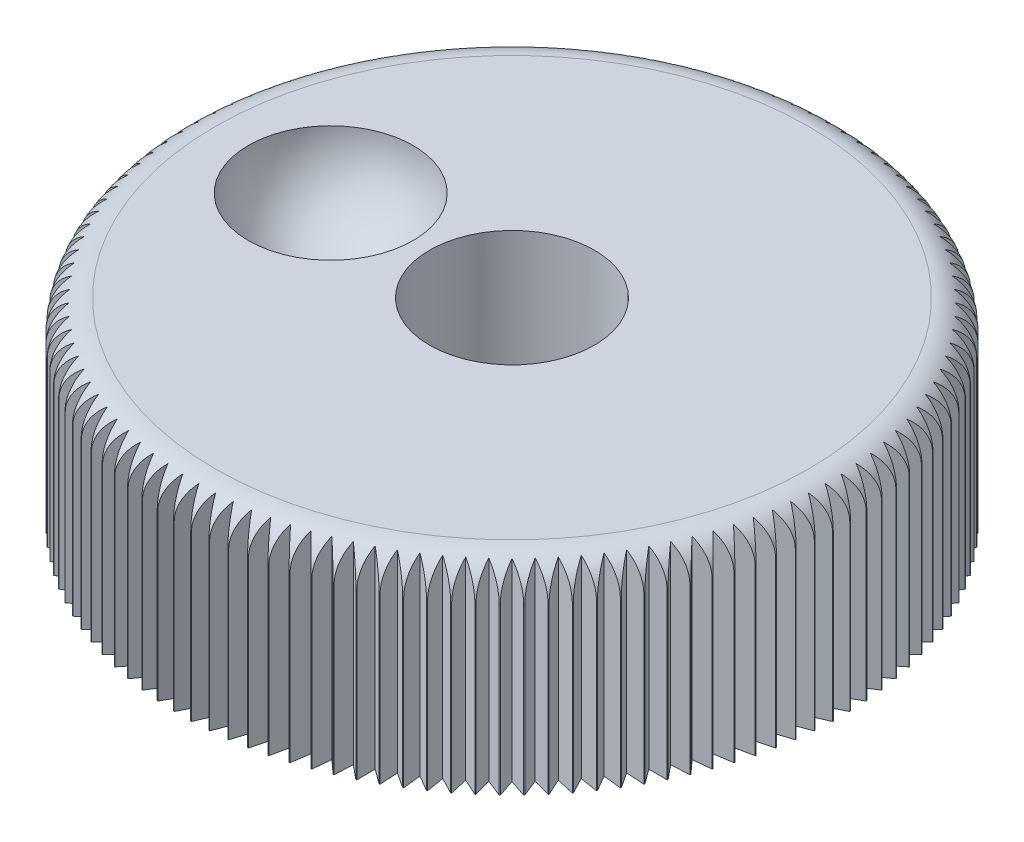
SolidWorks part; units mm, degrees
ref_plane "Спереди" through (0, 0, 0) normal (0, 0, 1) x (1, 0, 0)
ref_plane "Сверху" through (0, 0, 0) normal (0, 1, 0) x (1, 0, 0)
ref_plane "Справа" through (0, 0, 0) normal (1, 0, 0) x (0, 0, -1)
sketch "Эскиз1" plane through (0, 0, 0) normal (0, 1, 0) x (1, 0, 0)
  circle A0 centre (0, 0) radius 6
  dimension "D1" = 12
extrude "Бобышка-Вытянуть1" add sketch "Эскиз1" along normal blind 10
ref_plane "Плоскость1" through (0, 7.5, 0) normal (0, 1, 0) x (1, 0, 0)
sketch "Эскиз2" plane through (0, 7.5, 0) normal (0, 1, 0) x (1, 0, 0)
  circle A0 centre (0, 0) radius 20
  dimension "D1" = 40
extrude "Бобышка-Вытянуть2" add sketch "Эскиз2" along normal blind 12
fillet "Скругление1" radius 2 1 edges at (0, 19.5, 20)
sketch "Эскиз3" plane through (0, 7.5, 0) normal (0, -1, 0) x (1, 0, 0)
  line L0 (0, -20) -> (0, 20) construction
  line L1 (0, -20) -> (0, -21) construction
  line L2 (0, -21) -> (-0.5, -19.9937)
  line L3 (0, -21) -> (0.5, -19.9937)
  line L4 (0.5, -19.9937) -> (0, -19)
  line L5 (0, -19) -> (-0.5, -19.9937)
  line L6 (-1.0991, -20.9712) -> (-0.5471, -19.9925)
  line L7 (-1.0991, -20.9712) -> (-1.5457, -19.9402)
  line L8 (-0.9944, -18.974) -> (-1.5457, -19.9402)
  line L9 (-0.5471, -19.9925) -> (-0.9944, -18.974)
  line L10 (-2.1951, -20.885) -> (-1.5927, -19.9365)
  line L11 (-2.1951, -20.885) -> (-2.5872, -19.832)
  line L12 (-1.986, -18.8959) -> (-2.5872, -19.832)
  line L13 (-1.5927, -19.9365) -> (-1.986, -18.8959)
  line L14 (-3.2851, -20.7415) -> (-2.6339, -19.8258)
  line L15 (-3.2851, -20.7415) -> (-3.6216, -19.6694)
  line L16 (-2.9723, -18.7661) -> (-3.6216, -19.6694)
  line L17 (-2.6339, -19.8258) -> (-2.9723, -18.7661)
  line L18 (-4.3661, -20.5411) -> (-3.6679, -19.6608)
  line L19 (-4.3661, -20.5411) -> (-4.646, -19.4529)
  line L20 (-3.9503, -18.5848) -> (-4.646, -19.4529)
  line L21 (-3.6679, -19.6608) -> (-3.9503, -18.5848)
  line L22 (-5.4352, -20.2844) -> (-4.6918, -19.4419)
  line L23 (-5.4352, -20.2844) -> (-5.6577, -19.1831)
  line L24 (-4.9176, -18.3526) -> (-5.6577, -19.1831)
  line L25 (-4.6918, -19.4419) -> (-4.9176, -18.3526)
  line L26 (-6.4894, -19.9722) -> (-5.7029, -19.1697)
  line L27 (-6.4894, -19.9722) -> (-6.6539, -18.8607)
  line L28 (-5.8713, -18.0701) -> (-6.6539, -18.8607)
  line L29 (-5.7029, -19.1697) -> (-5.8713, -18.0701)
  line L30 (-7.5257, -19.6052) -> (-6.6983, -18.845)
  line L31 (-7.5257, -19.6052) -> (-7.6319, -18.4866)
  line L32 (-6.809, -17.738) -> (-7.6319, -18.4866)
  line L33 (-6.6983, -18.845) -> (-6.809, -17.738)
  line L34 (-8.5415, -19.1845) -> (-7.6754, -18.4686)
  line L35 (-8.5415, -19.1845) -> (-8.589, -18.0618)
  line L36 (-7.728, -17.3574) -> (-8.589, -18.0618)
  line L37 (-7.6754, -18.4686) -> (-7.728, -17.3574)
  line L38 (-9.5338, -18.7111) -> (-8.6315, -18.0416)
  line L39 (-9.5338, -18.7111) -> (-9.5225, -17.5876)
  line L40 (-8.6258, -16.9291) -> (-9.5225, -17.5876)
  line L41 (-8.6315, -18.0416) -> (-8.6258, -16.9291)
  line L42 (-10.5, -18.1865) -> (-9.5639, -17.5651)
  line L43 (-10.5, -18.1865) -> (-10.4299, -17.0651)
  line L44 (-9.5, -16.4545) -> (-10.4299, -17.0651)
  line L45 (-9.5639, -17.5651) -> (-9.5, -16.4545)
  line L46 (-11.4374, -17.6121) -> (-10.47, -17.0405)
  line L47 (-11.4374, -17.6121) -> (-11.3087, -16.4958)
  line L48 (-10.3481, -15.9347) -> (-11.3087, -16.4958)
  line L49 (-10.47, -17.0405) -> (-10.3481, -15.9347)
  line L50 (-12.3435, -16.9894) -> (-11.3475, -16.4692)
  line L51 (-12.3435, -16.9894) -> (-12.1565, -15.8814)
  line L52 (-11.1679, -15.3713) -> (-12.1565, -15.8814)
  line L53 (-11.3475, -16.4692) -> (-11.1679, -15.3713)
  line L54 (-13.2157, -16.3201) -> (-12.1939, -15.8527)
  line L55 (-13.2157, -16.3201) -> (-12.971, -15.2234)
  line L56 (-11.9571, -14.7658) -> (-12.971, -15.2234)
  line L57 (-12.1939, -15.8527) -> (-11.9571, -14.7658)
  line L58 (-14.0517, -15.606) -> (-13.0069, -15.1928)
  line L59 (-14.0517, -15.606) -> (-13.75, -14.5237)
  line L60 (-12.7135, -14.1198) -> (-13.75, -14.5237)
  line L61 (-13.0069, -15.1928) -> (-12.7135, -14.1198)
  line L62 (-14.8492, -14.8492) -> (-13.7842, -14.4913)
  line L63 (-14.8492, -14.8492) -> (-14.4913, -13.7842)
  line L64 (-13.435, -13.435) -> (-14.4913, -13.7842)
  line L65 (-13.7842, -14.4913) -> (-13.435, -13.435)
  line L66 (-15.606, -14.0517) -> (-14.5237, -13.75)
  line L67 (-15.606, -14.0517) -> (-15.1928, -13.0069)
  line L68 (-14.1198, -12.7135) -> (-15.1928, -13.0069)
  line L69 (-14.5237, -13.75) -> (-14.1198, -12.7135)
  line L70 (-16.3201, -13.2157) -> (-15.2234, -12.971)
  line L71 (-16.3201, -13.2157) -> (-15.8527, -12.1939)
  line L72 (-14.7658, -11.9571) -> (-15.8527, -12.1939)
  line L73 (-15.2234, -12.971) -> (-14.7658, -11.9571)
  line L74 (-16.9894, -12.3435) -> (-15.8814, -12.1565)
  line L75 (-16.9894, -12.3435) -> (-16.4692, -11.3475)
  line L76 (-15.3713, -11.1679) -> (-16.4692, -11.3475)
  line L77 (-15.8814, -12.1565) -> (-15.3713, -11.1679)
  line L78 (-17.6121, -11.4374) -> (-16.4958, -11.3087)
  line L79 (-17.6121, -11.4374) -> (-17.0405, -10.47)
  line L80 (-15.9347, -10.3481) -> (-17.0405, -10.47)
  line L81 (-16.4958, -11.3087) -> (-15.9347, -10.3481)
  line L82 (-18.1865, -10.5) -> (-17.0651, -10.4299)
  line L83 (-18.1865, -10.5) -> (-17.5651, -9.5639)
  line L84 (-16.4545, -9.5) -> (-17.5651, -9.5639)
  line L85 (-17.0651, -10.4299) -> (-16.4545, -9.5)
  line L86 (-18.7111, -9.5338) -> (-17.5876, -9.5225)
  line L87 (-18.7111, -9.5338) -> (-18.0416, -8.6315)
  line L88 (-16.9291, -8.6258) -> (-18.0416, -8.6315)
  line L89 (-17.5876, -9.5225) -> (-16.9291, -8.6258)
  line L90 (-19.1845, -8.5415) -> (-18.0618, -8.589)
  line L91 (-19.1845, -8.5415) -> (-18.4686, -7.6754)
  line L92 (-17.3574, -7.728) -> (-18.4686, -7.6754)
  line L93 (-18.0618, -8.589) -> (-17.3574, -7.728)
  line L94 (-19.6052, -7.5257) -> (-18.4866, -7.6319)
  line L95 (-19.6052, -7.5257) -> (-18.845, -6.6983)
  line L96 (-17.738, -6.809) -> (-18.845, -6.6983)
  line L97 (-18.4866, -7.6319) -> (-17.738, -6.809)
  line L98 (-19.9722, -6.4894) -> (-18.8607, -6.6539)
  line L99 (-19.9722, -6.4894) -> (-19.1697, -5.7029)
  line L100 (-18.0701, -5.8713) -> (-19.1697, -5.7029)
  line L101 (-18.8607, -6.6539) -> (-18.0701, -5.8713)
  line L102 (-20.2844, -5.4352) -> (-19.1831, -5.6577)
  line L103 (-20.2844, -5.4352) -> (-19.4419, -4.6918)
  line L104 (-18.3526, -4.9176) -> (-19.4419, -4.6918)
  line L105 (-19.1831, -5.6577) -> (-18.3526, -4.9176)
  line L106 (-20.5411, -4.3661) -> (-19.4529, -4.646)
  line L107 (-20.5411, -4.3661) -> (-19.6608, -3.6679)
  line L108 (-18.5848, -3.9503) -> (-19.6608, -3.6679)
  line L109 (-19.4529, -4.646) -> (-18.5848, -3.9503)
  line L110 (-20.7415, -3.2851) -> (-19.6694, -3.6216)
  line L111 (-20.7415, -3.2851) -> (-19.8258, -2.6339)
  line L112 (-18.7661, -2.9723) -> (-19.8258, -2.6339)
  line L113 (-19.6694, -3.6216) -> (-18.7661, -2.9723)
  line L114 (-20.885, -2.1951) -> (-19.832, -2.5872)
  line L115 (-20.885, -2.1951) -> (-19.9365, -1.5927)
  line L116 (-18.8959, -1.986) -> (-19.9365, -1.5927)
  line L117 (-19.832, -2.5872) -> (-18.8959, -1.986)
  line L118 (-20.9712, -1.0991) -> (-19.9402, -1.5457)
  line L119 (-20.9712, -1.0991) -> (-19.9925, -0.5471)
  line L120 (-18.974, -0.9944) -> (-19.9925, -0.5471)
  line L121 (-19.9402, -1.5457) -> (-18.974, -0.9944)
  line L122 (-21, 0) -> (-19.9937, -0.5)
  line L123 (-21, 0) -> (-19.9937, 0.5)
  line L124 (-19, 0) -> (-19.9937, 0.5)
  line L125 (-19.9937, -0.5) -> (-19, 0)
  line L126 (-20.9712, 1.0991) -> (-19.9925, 0.5471)
  line L127 (-20.9712, 1.0991) -> (-19.9402, 1.5457)
  line L128 (-18.974, 0.9944) -> (-19.9402, 1.5457)
  line L129 (-19.9925, 0.5471) -> (-18.974, 0.9944)
  line L130 (-20.885, 2.1951) -> (-19.9365, 1.5927)
  line L131 (-20.885, 2.1951) -> (-19.832, 2.5872)
  line L132 (-18.8959, 1.986) -> (-19.832, 2.5872)
  line L133 (-19.9365, 1.5927) -> (-18.8959, 1.986)
  line L134 (-20.7415, 3.2851) -> (-19.8258, 2.6339)
  line L135 (-20.7415, 3.2851) -> (-19.6694, 3.6216)
  line L136 (-18.7661, 2.9723) -> (-19.6694, 3.6216)
  line L137 (-19.8258, 2.6339) -> (-18.7661, 2.9723)
  line L138 (-20.5411, 4.3661) -> (-19.6608, 3.6679)
  line L139 (-20.5411, 4.3661) -> (-19.4529, 4.646)
  line L140 (-18.5848, 3.9503) -> (-19.4529, 4.646)
  line L141 (-19.6608, 3.6679) -> (-18.5848, 3.9503)
  line L142 (-20.2844, 5.4352) -> (-19.4419, 4.6918)
  line L143 (-20.2844, 5.4352) -> (-19.1831, 5.6577)
  line L144 (-18.3526, 4.9176) -> (-19.1831, 5.6577)
  line L145 (-19.4419, 4.6918) -> (-18.3526, 4.9176)
  line L146 (-19.9722, 6.4894) -> (-19.1697, 5.7029)
  line L147 (-19.9722, 6.4894) -> (-18.8607, 6.6539)
  line L148 (-18.0701, 5.8713) -> (-18.8607, 6.6539)
  line L149 (-19.1697, 5.7029) -> (-18.0701, 5.8713)
  line L150 (-19.6052, 7.5257) -> (-18.845, 6.6983)
  line L151 (-19.6052, 7.5257) -> (-18.4866, 7.6319)
  line L152 (-17.738, 6.809) -> (-18.4866, 7.6319)
  line L153 (-18.845, 6.6983) -> (-17.738, 6.809)
  line L154 (-19.1845, 8.5415) -> (-18.4686, 7.6754)
  line L155 (-19.1845, 8.5415) -> (-18.0618, 8.589)
  line L156 (-17.3574, 7.728) -> (-18.0618, 8.589)
  line L157 (-18.4686, 7.6754) -> (-17.3574, 7.728)
  line L158 (-18.7111, 9.5338) -> (-18.0416, 8.6315)
  line L159 (-18.7111, 9.5338) -> (-17.5876, 9.5225)
  line L160 (-16.9291, 8.6258) -> (-17.5876, 9.5225)
  line L161 (-18.0416, 8.6315) -> (-16.9291, 8.6258)
  line L162 (-18.1865, 10.5) -> (-17.5651, 9.5639)
  line L163 (-18.1865, 10.5) -> (-17.0651, 10.4299)
  line L164 (-16.4545, 9.5) -> (-17.0651, 10.4299)
  line L165 (-17.5651, 9.5639) -> (-16.4545, 9.5)
  line L166 (-17.6121, 11.4374) -> (-17.0405, 10.47)
  line L167 (-17.6121, 11.4374) -> (-16.4958, 11.3087)
  line L168 (-15.9347, 10.3481) -> (-16.4958, 11.3087)
  line L169 (-17.0405, 10.47) -> (-15.9347, 10.3481)
  line L170 (-16.9894, 12.3435) -> (-16.4692, 11.3475)
  line L171 (-16.9894, 12.3435) -> (-15.8814, 12.1565)
  line L172 (-15.3713, 11.1679) -> (-15.8814, 12.1565)
  line L173 (-16.4692, 11.3475) -> (-15.3713, 11.1679)
  line L174 (-16.3201, 13.2157) -> (-15.8527, 12.1939)
  line L175 (-16.3201, 13.2157) -> (-15.2234, 12.971)
  line L176 (-14.7658, 11.9571) -> (-15.2234, 12.971)
  line L177 (-15.8527, 12.1939) -> (-14.7658, 11.9571)
  line L178 (-15.606, 14.0517) -> (-15.1928, 13.0069)
  line L179 (-15.606, 14.0517) -> (-14.5237, 13.75)
  line L180 (-14.1198, 12.7135) -> (-14.5237, 13.75)
  line L181 (-15.1928, 13.0069) -> (-14.1198, 12.7135)
  line L182 (-14.8492, 14.8492) -> (-14.4913, 13.7842)
  line L183 (-14.8492, 14.8492) -> (-13.7842, 14.4913)
  line L184 (-13.435, 13.435) -> (-13.7842, 14.4913)
  line L185 (-14.4913, 13.7842) -> (-13.435, 13.435)
  line L186 (-14.0517, 15.606) -> (-13.75, 14.5237)
  line L187 (-14.0517, 15.606) -> (-13.0069, 15.1928)
  line L188 (-12.7135, 14.1198) -> (-13.0069, 15.1928)
  line L189 (-13.75, 14.5237) -> (-12.7135, 14.1198)
  line L190 (-13.2157, 16.3201) -> (-12.971, 15.2234)
  line L191 (-13.2157, 16.3201) -> (-12.1939, 15.8527)
  line L192 (-11.9571, 14.7658) -> (-12.1939, 15.8527)
  line L193 (-12.971, 15.2234) -> (-11.9571, 14.7658)
  line L194 (-12.3435, 16.9894) -> (-12.1565, 15.8814)
  line L195 (-12.3435, 16.9894) -> (-11.3475, 16.4692)
  line L196 (-11.1679, 15.3713) -> (-11.3475, 16.4692)
  line L197 (-12.1565, 15.8814) -> (-11.1679, 15.3713)
  line L198 (-11.4374, 17.6121) -> (-11.3087, 16.4958)
  line L199 (-11.4374, 17.6121) -> (-10.47, 17.0405)
  line L200 (-10.3481, 15.9347) -> (-10.47, 17.0405)
  line L201 (-11.3087, 16.4958) -> (-10.3481, 15.9347)
  line L202 (-10.5, 18.1865) -> (-10.4299, 17.0651)
  line L203 (-10.5, 18.1865) -> (-9.5639, 17.5651)
  line L204 (-9.5, 16.4545) -> (-9.5639, 17.5651)
  line L205 (-10.4299, 17.0651) -> (-9.5, 16.4545)
  line L206 (-9.5338, 18.7111) -> (-9.5225, 17.5876)
  line L207 (-9.5338, 18.7111) -> (-8.6315, 18.0416)
  line L208 (-8.6258, 16.9291) -> (-8.6315, 18.0416)
  line L209 (-9.5225, 17.5876) -> (-8.6258, 16.9291)
  line L210 (-8.5415, 19.1845) -> (-8.589, 18.0618)
  line L211 (-8.5415, 19.1845) -> (-7.6754, 18.4686)
  line L212 (-7.728, 17.3574) -> (-7.6754, 18.4686)
  line L213 (-8.589, 18.0618) -> (-7.728, 17.3574)
  line L214 (-7.5257, 19.6052) -> (-7.6319, 18.4866)
  line L215 (-7.5257, 19.6052) -> (-6.6983, 18.845)
  line L216 (-6.809, 17.738) -> (-6.6983, 18.845)
  line L217 (-7.6319, 18.4866) -> (-6.809, 17.738)
  line L218 (-6.4894, 19.9722) -> (-6.6539, 18.8607)
  line L219 (-6.4894, 19.9722) -> (-5.7029, 19.1697)
  line L220 (-5.8713, 18.0701) -> (-5.7029, 19.1697)
  line L221 (-6.6539, 18.8607) -> (-5.8713, 18.0701)
  line L222 (-5.4352, 20.2844) -> (-5.6577, 19.1831)
  line L223 (-5.4352, 20.2844) -> (-4.6918, 19.4419)
  line L224 (-4.9176, 18.3526) -> (-4.6918, 19.4419)
  line L225 (-5.6577, 19.1831) -> (-4.9176, 18.3526)
  line L226 (-4.3661, 20.5411) -> (-4.646, 19.4529)
  line L227 (-4.3661, 20.5411) -> (-3.6679, 19.6608)
  line L228 (-3.9503, 18.5848) -> (-3.6679, 19.6608)
  line L229 (-4.646, 19.4529) -> (-3.9503, 18.5848)
  line L230 (-3.2851, 20.7415) -> (-3.6216, 19.6694)
  line L231 (-3.2851, 20.7415) -> (-2.6339, 19.8258)
  line L232 (-2.9723, 18.7661) -> (-2.6339, 19.8258)
  line L233 (-3.6216, 19.6694) -> (-2.9723, 18.7661)
  line L234 (-2.1951, 20.885) -> (-2.5872, 19.832)
  line L235 (-2.1951, 20.885) -> (-1.5927, 19.9365)
  line L236 (-1.986, 18.8959) -> (-1.5927, 19.9365)
  line L237 (-2.5872, 19.832) -> (-1.986, 18.8959)
  line L238 (-1.0991, 20.9712) -> (-1.5457, 19.9402)
  line L239 (-1.0991, 20.9712) -> (-0.5471, 19.9925)
  line L240 (-0.9944, 18.974) -> (-0.5471, 19.9925)
  line L241 (-1.5457, 19.9402) -> (-0.9944, 18.974)
  line L242 (0, 21) -> (-0.5, 19.9937)
  line L243 (0, 21) -> (0.5, 19.9937)
  line L244 (0, 19) -> (0.5, 19.9937)
  line L245 (-0.5, 19.9937) -> (0, 19)
  line L246 (1.0991, 20.9712) -> (0.5471, 19.9925)
  line L247 (1.0991, 20.9712) -> (1.5457, 19.9402)
  line L248 (0.9944, 18.974) -> (1.5457, 19.9402)
  line L249 (0.5471, 19.9925) -> (0.9944, 18.974)
  line L250 (2.1951, 20.885) -> (1.5927, 19.9365)
  line L251 (2.1951, 20.885) -> (2.5872, 19.832)
  line L252 (1.986, 18.8959) -> (2.5872, 19.832)
  line L253 (1.5927, 19.9365) -> (1.986, 18.8959)
  line L254 (3.2851, 20.7415) -> (2.6339, 19.8258)
  line L255 (3.2851, 20.7415) -> (3.6216, 19.6694)
  line L256 (2.9723, 18.7661) -> (3.6216, 19.6694)
  line L257 (2.6339, 19.8258) -> (2.9723, 18.7661)
  line L258 (4.3661, 20.5411) -> (3.6679, 19.6608)
  line L259 (4.3661, 20.5411) -> (4.646, 19.4529)
  line L260 (3.9503, 18.5848) -> (4.646, 19.4529)
  line L261 (3.6679, 19.6608) -> (3.9503, 18.5848)
  line L262 (5.4352, 20.2844) -> (4.6918, 19.4419)
  line L263 (5.4352, 20.2844) -> (5.6577, 19.1831)
  line L264 (4.9176, 18.3526) -> (5.6577, 19.1831)
  line L265 (4.6918, 19.4419) -> (4.9176, 18.3526)
  line L266 (6.4894, 19.9722) -> (5.7029, 19.1697)
  line L267 (6.4894, 19.9722) -> (6.6539, 18.8607)
  line L268 (5.8713, 18.0701) -> (6.6539, 18.8607)
  line L269 (5.7029, 19.1697) -> (5.8713, 18.0701)
  line L270 (7.5257, 19.6052) -> (6.6983, 18.845)
  line L271 (7.5257, 19.6052) -> (7.6319, 18.4866)
  line L272 (6.809, 17.738) -> (7.6319, 18.4866)
  line L273 (6.6983, 18.845) -> (6.809, 17.738)
  line L274 (8.5415, 19.1845) -> (7.6754, 18.4686)
  line L275 (8.5415, 19.1845) -> (8.589, 18.0618)
  line L276 (7.728, 17.3574) -> (8.589, 18.0618)
  line L277 (7.6754, 18.4686) -> (7.728, 17.3574)
  line L278 (9.5338, 18.7111) -> (8.6315, 18.0416)
  line L279 (9.5338, 18.7111) -> (9.5225, 17.5876)
  line L280 (8.6258, 16.9291) -> (9.5225, 17.5876)
  line L281 (8.6315, 18.0416) -> (8.6258, 16.9291)
  line L282 (10.5, 18.1865) -> (9.5639, 17.5651)
  line L283 (10.5, 18.1865) -> (10.4299, 17.0651)
  line L284 (9.5, 16.4545) -> (10.4299, 17.0651)
  line L285 (9.5639, 17.5651) -> (9.5, 16.4545)
  line L286 (11.4374, 17.6121) -> (10.47, 17.0405)
  line L287 (11.4374, 17.6121) -> (11.3087, 16.4958)
  line L288 (10.3481, 15.9347) -> (11.3087, 16.4958)
  line L289 (10.47, 17.0405) -> (10.3481, 15.9347)
  line L290 (12.3435, 16.9894) -> (11.3475, 16.4692)
  line L291 (12.3435, 16.9894) -> (12.1565, 15.8814)
  line L292 (11.1679, 15.3713) -> (12.1565, 15.8814)
  line L293 (11.3475, 16.4692) -> (11.1679, 15.3713)
  line L294 (13.2157, 16.3201) -> (12.1939, 15.8527)
  line L295 (13.2157, 16.3201) -> (12.971, 15.2234)
  line L296 (11.9571, 14.7658) -> (12.971, 15.2234)
  line L297 (12.1939, 15.8527) -> (11.9571, 14.7658)
  line L298 (14.0517, 15.606) -> (13.0069, 15.1928)
  line L299 (14.0517, 15.606) -> (13.75, 14.5237)
  line L300 (12.7135, 14.1198) -> (13.75, 14.5237)
  line L301 (13.0069, 15.1928) -> (12.7135, 14.1198)
  line L302 (14.8492, 14.8492) -> (13.7842, 14.4913)
  line L303 (14.8492, 14.8492) -> (14.4913, 13.7842)
  line L304 (13.435, 13.435) -> (14.4913, 13.7842)
  line L305 (13.7842, 14.4913) -> (13.435, 13.435)
  line L306 (15.606, 14.0517) -> (14.5237, 13.75)
  line L307 (15.606, 14.0517) -> (15.1928, 13.0069)
  line L308 (14.1198, 12.7135) -> (15.1928, 13.0069)
  line L309 (14.5237, 13.75) -> (14.1198, 12.7135)
  line L310 (16.3201, 13.2157) -> (15.2234, 12.971)
  line L311 (16.3201, 13.2157) -> (15.8527, 12.1939)
  line L312 (14.7658, 11.9571) -> (15.8527, 12.1939)
  line L313 (15.2234, 12.971) -> (14.7658, 11.9571)
  line L314 (16.9894, 12.3435) -> (15.8814, 12.1565)
  line L315 (16.9894, 12.3435) -> (16.4692, 11.3475)
  line L316 (15.3713, 11.1679) -> (16.4692, 11.3475)
  line L317 (15.8814, 12.1565) -> (15.3713, 11.1679)
  line L318 (17.6121, 11.4374) -> (16.4958, 11.3087)
  line L319 (17.6121, 11.4374) -> (17.0405, 10.47)
  line L320 (15.9347, 10.3481) -> (17.0405, 10.47)
  line L321 (16.4958, 11.3087) -> (15.9347, 10.3481)
  line L322 (18.1865, 10.5) -> (17.0651, 10.4299)
  line L323 (18.1865, 10.5) -> (17.5651, 9.5639)
  line L324 (16.4545, 9.5) -> (17.5651, 9.5639)
  line L325 (17.0651, 10.4299) -> (16.4545, 9.5)
  line L326 (18.7111, 9.5338) -> (17.5876, 9.5225)
  line L327 (18.7111, 9.5338) -> (18.0416, 8.6315)
  line L328 (16.9291, 8.6258) -> (18.0416, 8.6315)
  line L329 (17.5876, 9.5225) -> (16.9291, 8.6258)
  line L330 (19.1845, 8.5415) -> (18.0618, 8.589)
  line L331 (19.1845, 8.5415) -> (18.4686, 7.6754)
  line L332 (17.3574, 7.728) -> (18.4686, 7.6754)
  line L333 (18.0618, 8.589) -> (17.3574, 7.728)
  line L334 (19.6052, 7.5257) -> (18.4866, 7.6319)
  line L335 (19.6052, 7.5257) -> (18.845, 6.6983)
  line L336 (17.738, 6.809) -> (18.845, 6.6983)
  line L337 (18.4866, 7.6319) -> (17.738, 6.809)
  line L338 (19.9722, 6.4894) -> (18.8607, 6.6539)
  line L339 (19.9722, 6.4894) -> (19.1697, 5.7029)
  line L340 (18.0701, 5.8713) -> (19.1697, 5.7029)
  line L341 (18.8607, 6.6539) -> (18.0701, 5.8713)
  line L342 (20.2844, 5.4352) -> (19.1831, 5.6577)
  line L343 (20.2844, 5.4352) -> (19.4419, 4.6918)
  line L344 (18.3526, 4.9176) -> (19.4419, 4.6918)
  line L345 (19.1831, 5.6577) -> (18.3526, 4.9176)
  line L346 (20.5411, 4.3661) -> (19.4529, 4.646)
  line L347 (20.5411, 4.3661) -> (19.6608, 3.6679)
  line L348 (18.5848, 3.9503) -> (19.6608, 3.6679)
  line L349 (19.4529, 4.646) -> (18.5848, 3.9503)
  line L350 (20.7415, 3.2851) -> (19.6694, 3.6216)
  line L351 (20.7415, 3.2851) -> (19.8258, 2.6339)
  line L352 (18.7661, 2.9723) -> (19.8258, 2.6339)
  line L353 (19.6694, 3.6216) -> (18.7661, 2.9723)
  line L354 (20.885, 2.1951) -> (19.832, 2.5872)
  line L355 (20.885, 2.1951) -> (19.9365, 1.5927)
  line L356 (18.8959, 1.986) -> (19.9365, 1.5927)
  line L357 (19.832, 2.5872) -> (18.8959, 1.986)
  line L358 (20.9712, 1.0991) -> (19.9402, 1.5457)
  line L359 (20.9712, 1.0991) -> (19.9925, 0.5471)
  line L360 (18.974, 0.9944) -> (19.9925, 0.5471)
  line L361 (19.9402, 1.5457) -> (18.974, 0.9944)
  line L362 (21, 0) -> (19.9937, 0.5)
  line L363 (21, 0) -> (19.9937, -0.5)
  line L364 (19, 0) -> (19.9937, -0.5)
  line L365 (19.9937, 0.5) -> (19, 0)
  line L366 (20.9712, -1.0991) -> (19.9925, -0.5471)
  line L367 (20.9712, -1.0991) -> (19.9402, -1.5457)
  line L368 (18.974, -0.9944) -> (19.9402, -1.5457)
  line L369 (19.9925, -0.5471) -> (18.974, -0.9944)
  line L370 (20.885, -2.1951) -> (19.9365, -1.5927)
  line L371 (20.885, -2.1951) -> (19.832, -2.5872)
  line L372 (18.8959, -1.986) -> (19.832, -2.5872)
  line L373 (19.9365, -1.5927) -> (18.8959, -1.986)
  line L374 (20.7415, -3.2851) -> (19.8258, -2.6339)
  line L375 (20.7415, -3.2851) -> (19.6694, -3.6216)
  line L376 (18.7661, -2.9723) -> (19.6694, -3.6216)
  line L377 (19.8258, -2.6339) -> (18.7661, -2.9723)
  line L378 (20.5411, -4.3661) -> (19.6608, -3.6679)
  line L379 (20.5411, -4.3661) -> (19.4529, -4.646)
  line L380 (18.5848, -3.9503) -> (19.4529, -4.646)
  line L381 (19.6608, -3.6679) -> (18.5848, -3.9503)
  line L382 (20.2844, -5.4352) -> (19.4419, -4.6918)
  line L383 (20.2844, -5.4352) -> (19.1831, -5.6577)
  line L384 (18.3526, -4.9176) -> (19.1831, -5.6577)
  line L385 (19.4419, -4.6918) -> (18.3526, -4.9176)
  line L386 (19.9722, -6.4894) -> (19.1697, -5.7029)
  line L387 (19.9722, -6.4894) -> (18.8607, -6.6539)
  line L388 (18.0701, -5.8713) -> (18.8607, -6.6539)
  line L389 (19.1697, -5.7029) -> (18.0701, -5.8713)
  line L390 (19.6052, -7.5257) -> (18.845, -6.6983)
  line L391 (19.6052, -7.5257) -> (18.4866, -7.6319)
  line L392 (17.738, -6.809) -> (18.4866, -7.6319)
  line L393 (18.845, -6.6983) -> (17.738, -6.809)
  line L394 (19.1845, -8.5415) -> (18.4686, -7.6754)
  line L395 (19.1845, -8.5415) -> (18.0618, -8.589)
  line L396 (17.3574, -7.728) -> (18.0618, -8.589)
  line L397 (18.4686, -7.6754) -> (17.3574, -7.728)
  line L398 (18.7111, -9.5338) -> (18.0416, -8.6315)
  line L399 (18.7111, -9.5338) -> (17.5876, -9.5225)
  line L400 (16.9291, -8.6258) -> (17.5876, -9.5225)
  line L401 (18.0416, -8.6315) -> (16.9291, -8.6258)
  line L402 (18.1865, -10.5) -> (17.5651, -9.5639)
  line L403 (18.1865, -10.5) -> (17.0651, -10.4299)
  line L404 (16.4545, -9.5) -> (17.0651, -10.4299)
  line L405 (17.5651, -9.5639) -> (16.4545, -9.5)
  line L406 (17.6121, -11.4374) -> (17.0405, -10.47)
  line L407 (17.6121, -11.4374) -> (16.4958, -11.3087)
  line L408 (15.9347, -10.3481) -> (16.4958, -11.3087)
  line L409 (17.0405, -10.47) -> (15.9347, -10.3481)
  line L410 (16.9894, -12.3435) -> (16.4692, -11.3475)
  line L411 (16.9894, -12.3435) -> (15.8814, -12.1565)
  line L412 (15.3713, -11.1679) -> (15.8814, -12.1565)
  line L413 (16.4692, -11.3475) -> (15.3713, -11.1679)
  line L414 (16.3201, -13.2157) -> (15.8527, -12.1939)
  line L415 (16.3201, -13.2157) -> (15.2234, -12.971)
  line L416 (14.7658, -11.9571) -> (15.2234, -12.971)
  line L417 (15.8527, -12.1939) -> (14.7658, -11.9571)
  line L418 (15.606, -14.0517) -> (15.1928, -13.0069)
  line L419 (15.606, -14.0517) -> (14.5237, -13.75)
  line L420 (14.1198, -12.7135) -> (14.5237, -13.75)
  line L421 (15.1928, -13.0069) -> (14.1198, -12.7135)
  line L422 (14.8492, -14.8492) -> (14.4913, -13.7842)
  line L423 (14.8492, -14.8492) -> (13.7842, -14.4913)
  line L424 (13.435, -13.435) -> (13.7842, -14.4913)
  line L425 (14.4913, -13.7842) -> (13.435, -13.435)
  line L426 (14.0517, -15.606) -> (13.75, -14.5237)
  line L427 (14.0517, -15.606) -> (13.0069, -15.1928)
  line L428 (12.7135, -14.1198) -> (13.0069, -15.1928)
  line L429 (13.75, -14.5237) -> (12.7135, -14.1198)
  line L430 (13.2157, -16.3201) -> (12.971, -15.2234)
  line L431 (13.2157, -16.3201) -> (12.1939, -15.8527)
  line L432 (11.9571, -14.7658) -> (12.1939, -15.8527)
  line L433 (12.971, -15.2234) -> (11.9571, -14.7658)
  line L434 (12.3435, -16.9894) -> (12.1565, -15.8814)
  line L435 (12.3435, -16.9894) -> (11.3475, -16.4692)
  line L436 (11.1679, -15.3713) -> (11.3475, -16.4692)
  line L437 (12.1565, -15.8814) -> (11.1679, -15.3713)
  line L438 (11.4374, -17.6121) -> (11.3087, -16.4958)
  line L439 (11.4374, -17.6121) -> (10.47, -17.0405)
  line L440 (10.3481, -15.9347) -> (10.47, -17.0405)
  line L441 (11.3087, -16.4958) -> (10.3481, -15.9347)
  line L442 (10.5, -18.1865) -> (10.4299, -17.0651)
  line L443 (10.5, -18.1865) -> (9.5639, -17.5651)
  line L444 (9.5, -16.4545) -> (9.5639, -17.5651)
  line L445 (10.4299, -17.0651) -> (9.5, -16.4545)
  line L446 (9.5338, -18.7111) -> (9.5225, -17.5876)
  line L447 (9.5338, -18.7111) -> (8.6315, -18.0416)
  line L448 (8.6258, -16.9291) -> (8.6315, -18.0416)
  line L449 (9.5225, -17.5876) -> (8.6258, -16.9291)
  line L450 (8.5415, -19.1845) -> (8.589, -18.0618)
  line L451 (8.5415, -19.1845) -> (7.6754, -18.4686)
  line L452 (7.728, -17.3574) -> (7.6754, -18.4686)
  line L453 (8.589, -18.0618) -> (7.728, -17.3574)
  line L454 (7.5257, -19.6052) -> (7.6319, -18.4866)
  line L455 (7.5257, -19.6052) -> (6.6983, -18.845)
  line L456 (6.809, -17.738) -> (6.6983, -18.845)
  line L457 (7.6319, -18.4866) -> (6.809, -17.738)
  line L458 (6.4894, -19.9722) -> (6.6539, -18.8607)
  line L459 (6.4894, -19.9722) -> (5.7029, -19.1697)
  line L460 (5.8713, -18.0701) -> (5.7029, -19.1697)
  line L461 (6.6539, -18.8607) -> (5.8713, -18.0701)
  line L462 (5.4352, -20.2844) -> (5.6577, -19.1831)
  line L463 (5.4352, -20.2844) -> (4.6918, -19.4419)
  line L464 (4.9176, -18.3526) -> (4.6918, -19.4419)
  line L465 (5.6577, -19.1831) -> (4.9176, -18.3526)
  line L466 (4.3661, -20.5411) -> (4.646, -19.4529)
  line L467 (4.3661, -20.5411) -> (3.6679, -19.6608)
  line L468 (3.9503, -18.5848) -> (3.6679, -19.6608)
  line L469 (4.646, -19.4529) -> (3.9503, -18.5848)
  line L470 (3.2851, -20.7415) -> (3.6216, -19.6694)
  line L471 (3.2851, -20.7415) -> (2.6339, -19.8258)
  line L472 (2.9723, -18.7661) -> (2.6339, -19.8258)
  line L473 (3.6216, -19.6694) -> (2.9723, -18.7661)
  line L474 (2.1951, -20.885) -> (2.5872, -19.832)
  line L475 (2.1951, -20.885) -> (1.5927, -19.9365)
  line L476 (1.986, -18.8959) -> (1.5927, -19.9365)
  line L477 (2.5872, -19.832) -> (1.986, -18.8959)
  line L478 (1.0991, -20.9712) -> (1.5457, -19.9402)
  line L479 (1.0991, -20.9712) -> (0.5471, -19.9925)
  line L480 (0.9944, -18.974) -> (0.5471, -19.9925)
  line L481 (1.5457, -19.9402) -> (0.9944, -18.974)
  circle A0 centre (0, 0) radius 20 construction
  point P489 (0, 0)
  dimension "D1" = 1
  dimension "D3" = 1
  dimension "D2" = 1
  dimension "D4" = 120
extrude "Вырез-Вытянуть1" cut sketch "Эскиз3" against normal through all and the other way through all
sketch "Эскиз4" plane through (0, 19.5, 0) normal (0, 1, 0) x (1, 0, 0)
  line L0 (-18, 0) -> (18, 0) construction
  line L1 (-16, 0) -> (-6, 0)
  circle A0 centre (0, 0) radius 18 construction
  arc A1 (-16, 0) -> (-6, 0) centre (-11, 0) cw
  dimension "D1" = 10
  dimension "D2" = 2
revolve "Вырез-Повернуть1" cut sketch "Эскиз4" angle 360 about L1
sketch "Эскиз5" plane through (0, 0, 0) normal (0, -1, 0) x (1, 0, 0)
  circle A0 centre (0, 0) radius 3.305
  dimension "D1" = 6.61
extrude "Вырез-Вытянуть2" cut sketch "Эскиз5" against normal blind 10
sketch "Эскиз6" plane through (0, 10, 0) normal (0, -1, 0) x (1, 0, 0)
  circle A0 centre (0, 0) radius 1.825
  dimension "D1" = 3.65
extrude "Вырез-Вытянуть3" cut sketch "Эскиз6" against normal through all
sketch "Эскиз7" plane through (0, 19.5, 0) normal (0, 1, 0) x (1, 0, 0)
  circle A0 centre (0, 0) radius 5
  dimension "D1" = 10
extrude "Вырез-Вытянуть4" cut sketch "Эскиз7" against normal offset from surface (7.5 mm away) 2
